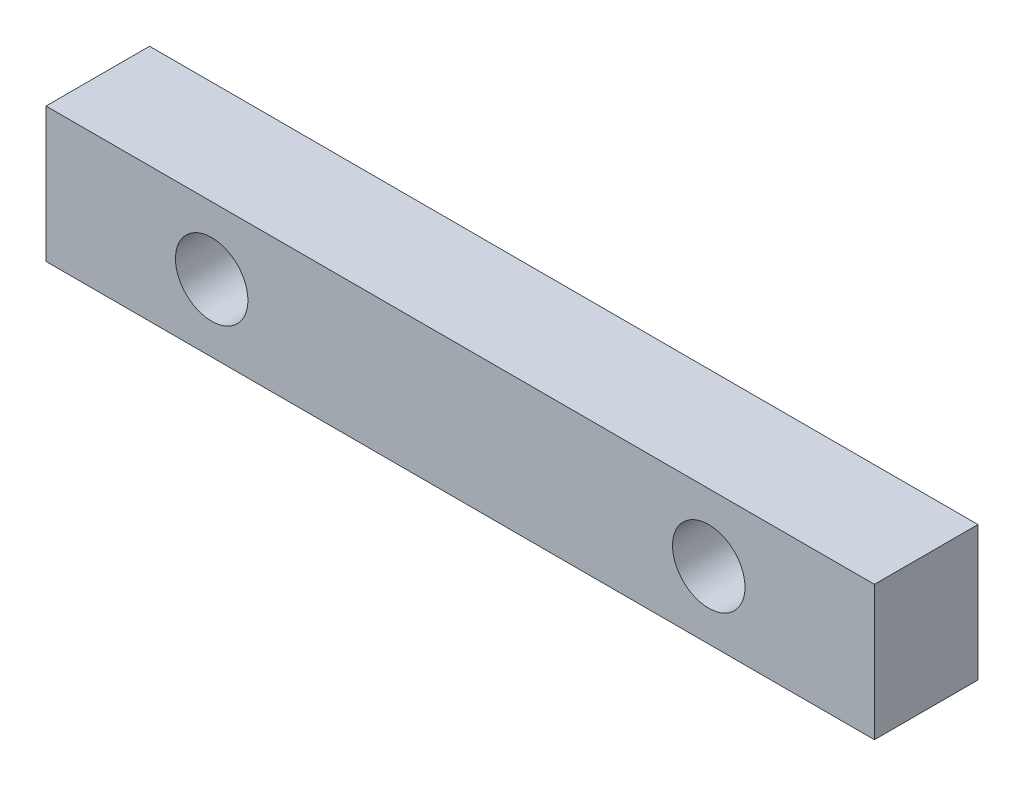
SolidWorks part; units mm, degrees
ref_plane "Front Plane" through (0, 0, 0) normal (0, 0, 1) x (1, 0, 0)
ref_plane "Top Plane" through (0, 0, 0) normal (0, 1, 0) x (1, 0, 0)
ref_plane "Right Plane" through (0, 0, 0) normal (1, 0, 0) x (0, 0, -1)
sketch "Sketch2" plane through (0, 0, 0) normal (0, 0, 1) x (1, 0, 0)
  line L0 (20, 0) -> (-20, 0) construction
  line L1 (-20, 3.25) -> (20, 3.25)
  line L2 (-20, 3.25) -> (-20, -3.25)
  line L3 (-20, -3.25) -> (20, -3.25)
  line L4 (20, 3.25) -> (20, -3.25)
  line L5 (-20, 3.25) -> (20, -3.25) construction
  line L6 (-20, -3.25) -> (20, 3.25) construction
  circle A0 centre (-12, 0) radius 1.75
  circle A1 centre (12, 0) radius 1.75
  point P0 (0, 0)
  dimension "D3" = 3.5
  dimension "D4" = 3.5
  dimension "D1" = 6.5
  dimension "D2" = 40
  dimension "D5" = 12
  dimension "D6" = 12
extrude "Boss-Extrude1" add sketch "Sketch2" along normal blind 5
